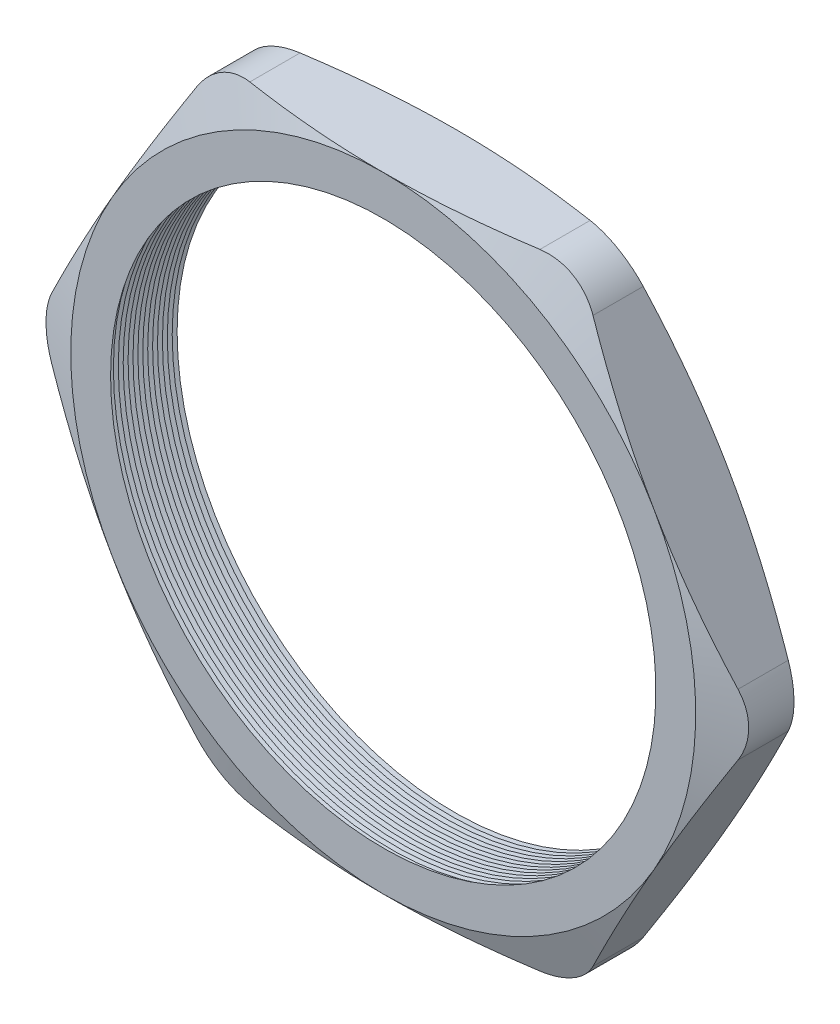
SolidWorks part; units mm, degrees
ref_plane "Front Plane" through (0, 0, 0) normal (0, 0, 1) x (1, 0, 0)
ref_plane "Top Plane" through (0, 0, 0) normal (0, 1, 0) x (1, 0, 0)
ref_plane "Right Plane" through (0, 0, 0) normal (1, 0, 0) x (0, 0, -1)
sketch "Sketch1" plane through (0, 0, 0) normal (0, 0, 1) x (1, 0, 0)
  line L1 (-14.958, 0) -> (-7.479, -12.954)
  line L2 (-7.479, -12.954) -> (7.479, -12.954)
  line L3 (7.479, -12.954) -> (14.958, 0)
  line L4 (14.958, 0) -> (7.479, 12.954)
  line L5 (7.479, 12.954) -> (-7.479, 12.954)
  line L6 (-7.479, 12.954) -> (-14.958, 0)
  circle A0 centre (0, 0) radius 12.954 construction
  circle A1 centre (0, 0) radius 11.303
  dimension "TS" = 22.606
  dimension "H" = 25.908
extrude "Extrude1" add sketch "Sketch1" along normal blind 3.048
fillet "Fillet1" radius 2.54 6 edges at (-7.479, 12.954, 1.524) (-14.958, 0, 1.524) (-7.479, -12.954, 1.524) (7.479, -12.954, 1.524) (14.958, 0, 1.524) (7.479, 12.954, 1.524)
sketch "Sketch2" plane through (0, 0, 3.048) normal (0, 0, 1) x (1, 0, 0)
  line L0 (6.0125, 12.954) -> (-6.0125, 12.954) construction
  circle A0 centre (0, 0) radius 12.954
extrude "Cut-Extrude1" cut sketch "Sketch2" against normal through all draft 70 flip side to cut
sketch "Sketch3" plane through (0, 0, 0) normal (0, 0, -1) x (-1, 0, 0)
  circle A0 centre (0, 0) radius 12.954
extrude "Cut-Extrude2" cut sketch "Sketch3" against normal through all draft 70 flip side to cut
sketch "Sketch4" plane through (0, 0, 0) normal (0, 1, 0) x (1, 0, 0)
  line L0 (-11.303, -3.048) -> (-11.303, -2.6081)
  line L2 (-11.303, -2.6081) -> (-11.684, -2.828)
  line L3 (-11.684, -2.828) -> (-11.303, -3.048)
  line L5 (-11.303, 0) -> (-11.303, -3.048) construction
  line L6 (-11.303, -3.048) -> (11.303, -3.048) construction
  dimension "D1" = 60
  dimension "D2" = 60
  dimension "D3" = 0.381
revolve "Cut-Revolve1" cut sketch "Sketch4" angle 360 about axis through (0, 0, 3.048) along (0, 0, -1)
pattern_linear "LPattern1" count 15 spacing 0.2032 along (0, 0, -1) of "Cut-Revolve1"
